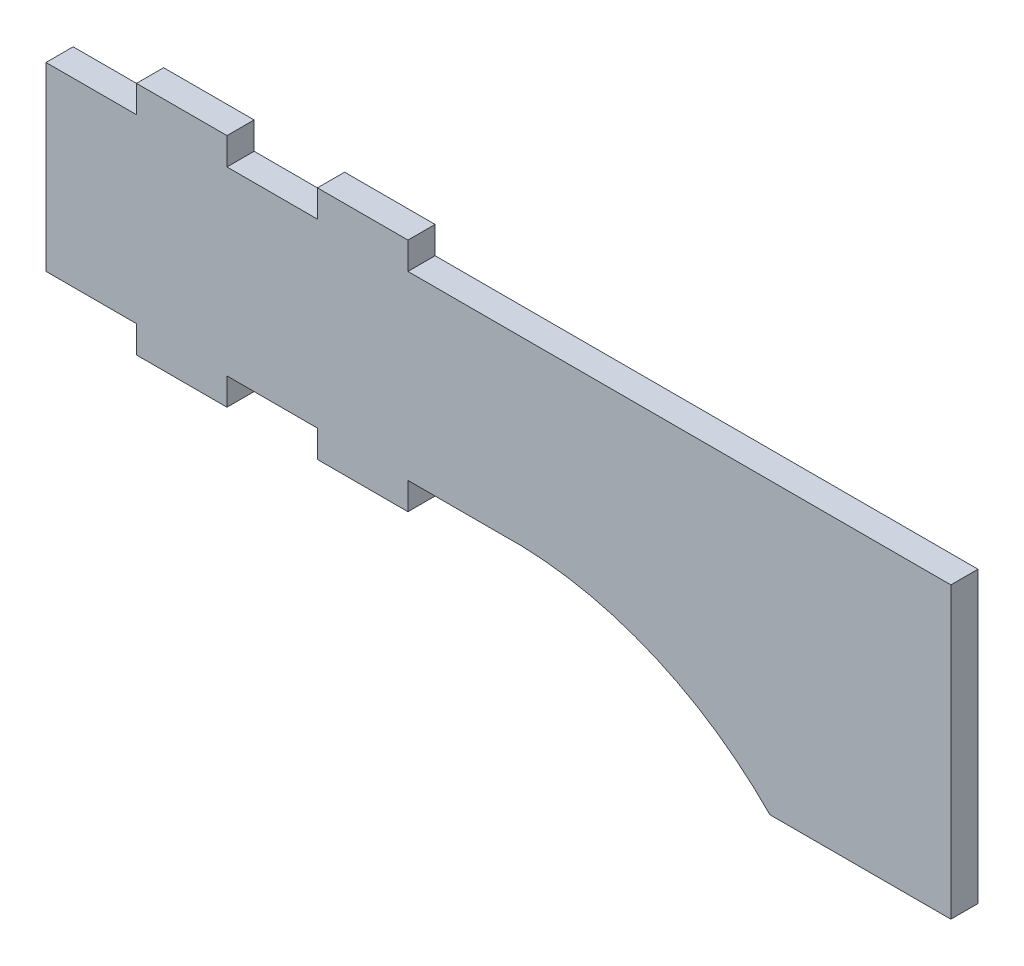
SolidWorks part; units mm, degrees
ref_plane "Front Plane" through (0, 0, 0) normal (0, 0, 1) x (1, 0, 0)
ref_plane "Top Plane" through (0, 0, 0) normal (0, 1, 0) x (1, 0, 0)
ref_plane "Right Plane" through (0, 0, 0) normal (1, 0, 0) x (0, 0, -1)
sketch "Sketch2" plane through (0, 0, 0) normal (0, 0, 1) x (1, 0, 0)
  line L0 (-27.5172, -1.3704) -> (-27.5172, 8.6296)
  line L1 (-27.5172, 8.6296) -> (-22.5172, 8.6296)
  line L2 (-22.5172, 8.6296) -> (-22.5172, 10.1296)
  line L3 (-22.5172, 10.1296) -> (-17.5172, 10.1296)
  line L4 (-17.5172, 10.1296) -> (-17.5172, 8.6296)
  line L5 (-17.5172, 8.6296) -> (-12.5172, 8.6296)
  line L6 (-12.5172, 8.6296) -> (-12.5172, 10.1296)
  line L7 (-12.5172, 10.1296) -> (-7.5172, 10.1296)
  line L8 (-7.5172, 10.1296) -> (-7.5172, 8.6296)
  line L9 (-7.5172, 8.6296) -> (22.4828, 8.6296)
  line L10 (22.4828, 8.6296) -> (22.4828, -7.3704)
  line L11 (22.4828, -7.3704) -> (12.4828, -7.3704)
  line L12 (-27.5172, -1.3704) -> (-22.5172, -1.3704)
  line L13 (-22.5172, -1.3704) -> (-22.5172, -2.8704)
  line L14 (-22.5172, -2.8704) -> (-17.5172, -2.8704)
  line L15 (-17.5172, -2.8704) -> (-17.5172, -1.3704)
  line L16 (-17.5172, -1.3704) -> (-12.5172, -1.3704)
  line L17 (-12.5172, -1.3704) -> (-12.5172, -2.8704)
  line L18 (-12.5172, -2.8704) -> (-7.5172, -2.8704)
  line L19 (-7.5172, -2.8704) -> (-7.5172, -1.3704)
  line L20 (-7.5172, -1.3704) -> (-2.5172, -1.3704)
  arc A0 (-2.5172, -1.3704) -> (12.4828, -7.3704) centre (-1.8122, -21.358) cw
  point P14 (2.3604, -11.392)
  dimension "D9" = 20
  dimension "D1" = 1.5
  dimension "D2" = 5
  dimension "D3" = 5
  dimension "D4" = 10
  dimension "D5" = 5
  dimension "D6" = 30
  dimension "D7" = 5
  dimension "D8" = 10
  dimension "D10" = 16
  dimension "D11" = 1.5
extrude "Boss-Extrude1" add sketch "Sketch2" along normal blind 1.5
